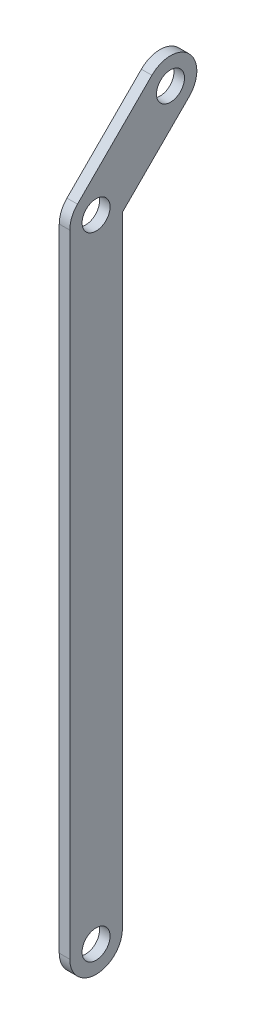
SolidWorks part; units mm, degrees
material "1060 Alloy"
ref_plane "Front Plane" through (0, 0, 0) normal (0, 0, 1) x (1, 0, 0)
ref_plane "Top Plane" through (0, 0, 0) normal (0, 1, 0) x (1, 0, 0)
ref_plane "Right Plane" through (0, 0, 0) normal (1, 0, 0) x (0, 0, -1)
sketch "Sketch1" plane through (0, 0, 0) normal (1, 0, 0) x (0, 0, -1)
  line L11 (0, 0) -> (0, -152.4) construction
  line L12 (6.35, -2.6303) -> (6.35, -152.4)
  line L13 (-6.35, 0) -> (-6.35, -152.4)
  line L14 (0, 0) -> (17.9605, 17.9605) construction
  line L15 (-4.4901, 4.4901) -> (13.4704, 22.4506)
  line L16 (6.35, -2.6303) -> (22.4506, 13.4704)
  arc A5 (-4.4901, 4.4901) -> (-6.35, 0) centre (0, 0) ccw
  arc A6 (-6.35, -152.4) -> (6.35, -152.4) centre (0, -152.4) ccw
  arc A8 (22.4506, 13.4704) -> (13.4704, 22.4506) centre (17.9605, 17.9605) ccw
  point P2 (0, 0)
  point P3 (-6.35, -152.4)
  point P7 (6.35, -152.4)
  point P12 (-6.35, 0)
  point P14 (-4.4901, 4.4901)
  point P16 (6.35, -2.6303)
  point P17 (22.4506, 13.4704)
  point P19 (13.4704, 22.4506)
  point P20 (0, 0)
  dimension "D1" = 152.4
  dimension "D2" = 6.35
  dimension "D4" = 135
  dimension "D3" = 25.4
extrude "Boss-Extrude1" add sketch "Sketch1" along normal blind 2.54
hole_wizard "1/4 Clearance Hole2" positions "Sketch4" profile "Sketch5" hole size "1/4" standard "ANSI Inch"
sketch "Sketch4" plane through (2.54, 0, 0) normal (1, 0, 0) x (0, 0, -1)
  point P0 (0, 0)
  point P3 (0, -152.4)
  point P7 (17.9605, 17.9605)
sketch "Sketch5" plane through (2.54, 0, 0) normal (0, 1, 0) x (0, 0, -1)
  line L0 (0, 0) -> (0, 10.4118)
  line L1 (0, 10.4118) -> (3.3782, 8.382)
  line L2 (3.3782, 8.382) -> (3.3782, 0)
  line L5 (3.3782, 0) -> (0, 0)
  line L10 (0, 10.4118) -> (-3.3782, 8.382) construction
  line L11 (0, -6.35) -> (0, 107.95) construction
  dimension "Hole Dia." = 6.7564
  dimension "Hole Depth" = 8.382
  dimension "Drill Angle" = 118
